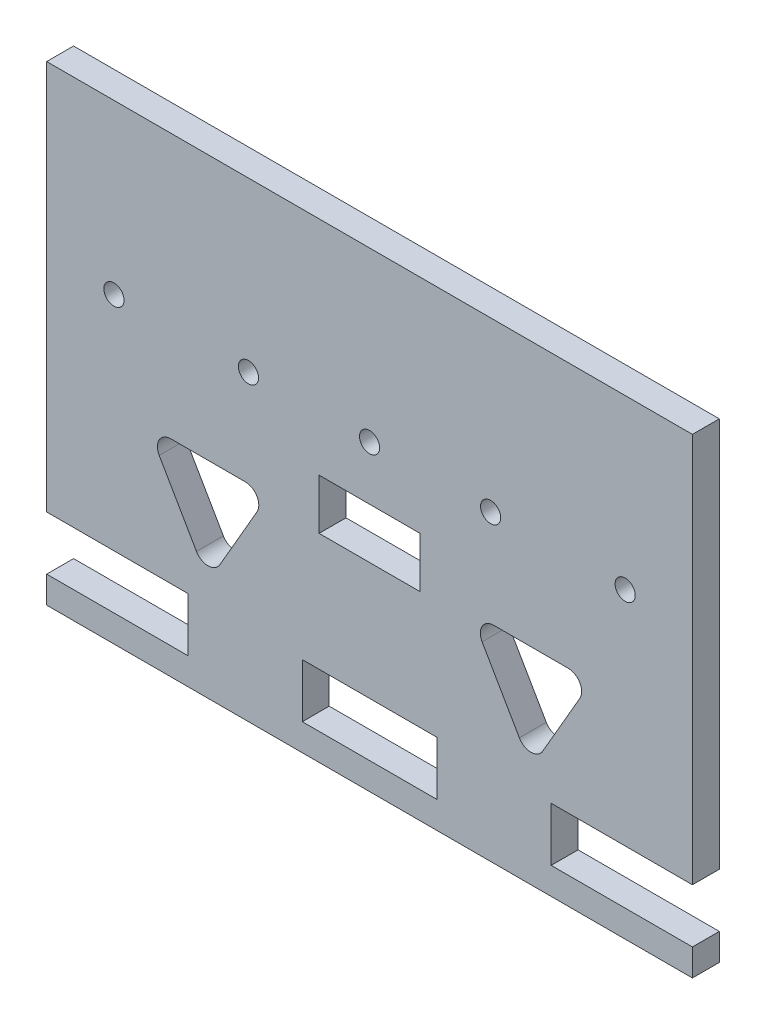
SolidWorks part; units mm, degrees
material "7075-T6, Chapa (SS)"
ref_plane "Plano frontal" through (0, 0, 0) normal (0, 0, 1) x (1, 0, 0)
ref_plane "Plano superior" through (0, 0, 0) normal (0, 1, 0) x (1, 0, 0)
ref_plane "Plano direito" through (0, 0, 0) normal (1, 0, 0) x (0, 0, -1)
sketch "Esboço1" plane through (0, 0, 0) normal (0, 0, 1) x (1, 0, 0)
  line L0 (48.005, 0) -> (48.005, -70) construction
  line L1 (0, 0) -> (96.01, 0)
  line L3 (0, -70) -> (96.01, -70)
  line L5 (38.005, -58) -> (58.005, -58)
  line L10 (58.005, -58) -> (58.005, -66)
  line L11 (58.005, -66) -> (38.005, -66)
  line L12 (40.505, -40.5) -> (55.505, -40.5)
  line L13 (55.505, -40.5) -> (55.505, -33)
  line L14 (55.505, -33) -> (40.505, -33)
  line L15 (38.005, -58) -> (38.005, -66)
  line L16 (40.505, -40.5) -> (40.505, -33)
  line L17 (0, -25) -> (96.01, -25) construction
  line L18 (0, -70) -> (0, -66)
  line L23 (0, -58) -> (21, -58)
  line L25 (0, -66) -> (21, -66)
  line L26 (21, -58) -> (21, -66)
  line L27 (75.01, -58) -> (96.01, -58)
  line L28 (75.01, -58) -> (75.01, -66)
  line L29 (75.01, -66) -> (96.01, -66)
  line L31 (0, 0) -> (0, -58)
  line L32 (96.01, -58) -> (96.01, 0)
  line L33 (96.01, -66) -> (96.01, -70)
  circle A0 centre (48.005, -25) radius 1.5
  circle A1 centre (86.01, -25) radius 1.5
  circle A2 centre (10, -25) radius 1.5
  circle A3 centre (66.01, -25) radius 1.5
  circle A4 centre (30, -25) radius 1.5
  point P11 (48.005, -58)
  point P17 (48.005, -66)
  point P18 (48.005, -40.5)
  point P19 (48.005, -33)
  point P39 (0, 0)
  point P40 (0, 0)
  dimension "D12" = 3
  dimension "D13" = 3
  dimension "D14" = 3
  dimension "D17" = 3
  dimension "D18" = 3
  dimension "D1" = 70
  dimension "D2" = 96.01
  dimension "D3" = 10
  dimension "D4" = 4
  dimension "D5" = 8
  dimension "D6" = 7.5
  dimension "D7" = 7.5
  dimension "D8" = 37
  dimension "D9" = 45
  dimension "D10" = 10
  dimension "D11" = 10
  dimension "D15" = 20
  dimension "D16" = 20
  dimension "D19" = 21
  dimension "D20" = 21
  dimension "D21" = 8
  dimension "D22" = 8
  dimension "D23" = 4
  dimension "D28" = 4
extrude "Ressalto-extrusão1" add sketch "Esboço1" along normal blind 4
sketch "Esboço2" plane through (0, 0, 4) normal (0, 0, 1) x (1, 0, 0)
  line L0 (63.01, -39.351) -> (81.01, -39.351)
  line L1 (81.01, -39.351) -> (72.01, -54.9395)
  line L2 (72.01, -54.9395) -> (63.01, -39.351)
  line L3 (15, -39.351) -> (33, -39.351)
  line L4 (33, -39.351) -> (24, -54.9395)
  line L5 (24, -54.9395) -> (15, -39.351)
  line L6 (96.01, -58) -> (96.01, 0) construction
  line L7 (0, 0) -> (0, -58) construction
  dimension "D1" = 18
  dimension "D2" = 15
  dimension "D3" = 15
extrude "Corte-extrusão1" cut sketch "Esboço2" against normal blind 10
fillet "Filete1" radius 2 6 edges at (24, -54.9395, 2) (15, -39.351, 2) (33, -39.351, 2) (72.01, -54.9395, 2) (63.01, -39.351, 2) (81.01, -39.351, 2)
sketch "Esboço3" plane through (0, -70, 0) normal (0, -1, 0) x (1, 0, 0)
  line L0 (0, 2) -> (96.01, 2) construction
  line L2 (0, 4) -> (0, 0) construction
  line L3 (96.01, 4) -> (96.01, 0) construction
  circle A0 centre (25, 2) radius 1.25
  circle A1 centre (34, 2) radius 1.25
  circle A2 centre (62.01, 2) radius 1.25
  circle A3 centre (71.01, 2) radius 1.25
  dimension "D1" = 2.5
  dimension "D2" = 2.5
  dimension "D3" = 2.5
  dimension "D4" = 2.5
  dimension "D5" = 25
  dimension "D6" = 9
  dimension "D8" = 25
  dimension "D7" = 9
extrude "Corte-extrusão2" cut sketch "Esboço3" against normal blind 12
